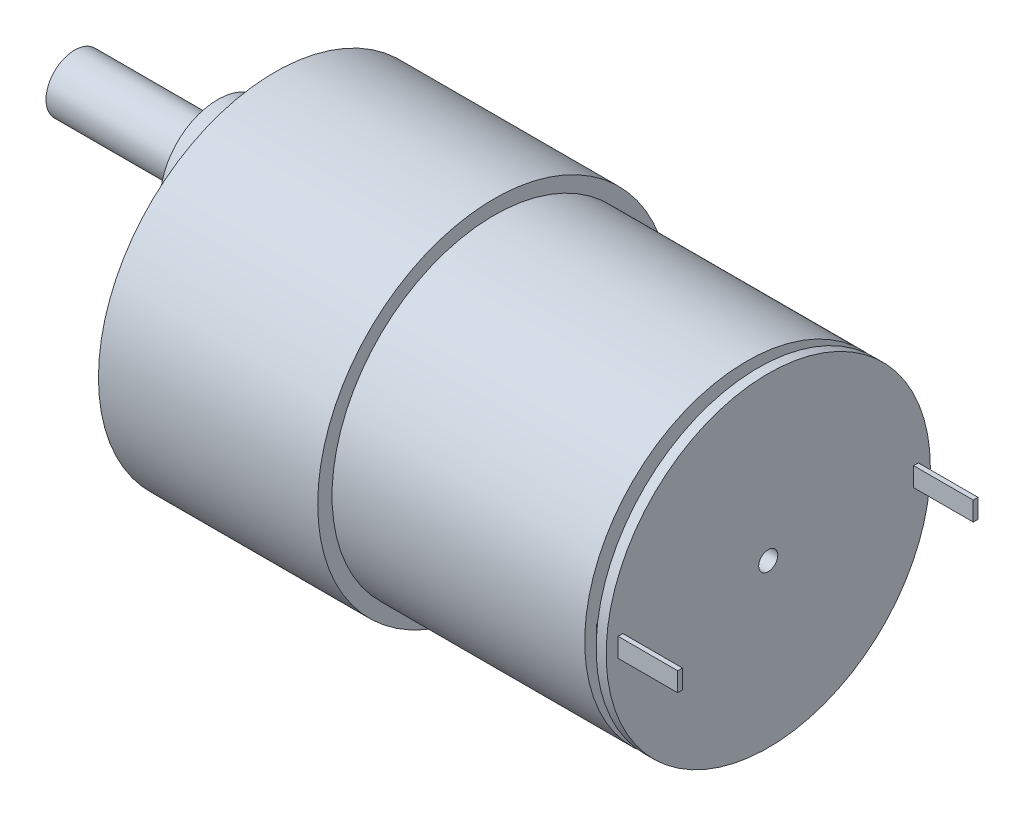
SolidWorks part; units mm, degrees
ref_plane "Front Plane" through (0, 0, 0) normal (0, 0, 1) x (1, 0, 0)
ref_plane "Top Plane" through (0, 0, 0) normal (0, 1, 0) x (1, 0, 0)
ref_plane "Right Plane" through (0, 0, 0) normal (1, 0, 0) x (0, 0, -1)
ref_plane "Plane1" through (41.25, 0, 0) normal (1, 0, 0) x (0, 0, -1)
sketch "Sketch1" plane through (41.25, 0, 0) normal (1, 0, 0) x (0, 0, -1)
  circle A0 centre (0, 0) radius 17
  dimension "D1" = 34
extrude "Boss-Extrude1" add sketch "Sketch1" against normal blind 1.05
sketch "Sketch2" plane through (40.2, 0, 0) normal (-1, 0, 0) x (0, 0, 1)
  line L0 (15.75, 1) -> (15.75, -1)
  line L1 (15.75, -1) -> (15.25, -1)
  line L2 (15.25, -1) -> (15.25, 1)
  line L3 (15.25, 1) -> (15.75, 1)
  line L4 (15.75, 1) -> (15.25, -1) construction
  line L5 (15.25, 1) -> (15.75, -1) construction
  line L6 (-15.25, 1) -> (-15.25, -1)
  line L7 (-15.25, -1) -> (-15.75, -1)
  line L8 (-15.75, -1) -> (-15.75, 1)
  line L9 (-15.75, 1) -> (-15.25, 1)
  line L10 (-15.25, 1) -> (-15.75, -1) construction
  line L11 (-15.75, 1) -> (-15.25, -1) construction
  circle A0 centre (0, 0) radius 15.5 construction
  point P7 (15.5, 0)
  point P12 (-15.5, 0)
  dimension "D3" = 31
  dimension "D1" = 2
  dimension "D2" = 0.5
extrude "Poles" add sketch "Sketch2" along normal blind 1.2 and the other way blind 7.3
sketch "Sketch3" plane through (40.2, 0, 0) normal (-1, 0, 0) x (0, 0, 1)
  circle A0 centre (0, 0) radius 1.5
extrude "Boss-Extrude3" add sketch "Sketch3" along normal blind 1.2
ref_plane "Plane2" through (39, 0, 0) normal (1, 0, 0) x (0, 0, -1)
sketch "Sketch5" plane through (39, 0, 0) normal (1, 0, 0) x (0, 0, -1)
  circle A2 centre (0, 0) radius 17
  dimension "D1" = 34
extrude "Boss-Extrude5" add sketch "Sketch5" against normal blind 26.5
ref_plane "Plane3" through (19, 0, 0) normal (1, 0, 0) x (0, 0, -1)
sketch "Sketch6" plane through (12.5, 0, 0) normal (1, 0, 0) x (0, 0, -1)
  circle A0 centre (0, 0) radius 18.5
  dimension "D1" = 37
extrude "Reductur" add sketch "Sketch6" against normal blind 21.5
sketch "Sketch35" plane through (-9, 0, 0) normal (-1, 0, 0) x (0, 0, 1)
  circle A0 centre (0, 0) radius 18.5
  circle A1 centre (0, 0) radius 18.5 construction
extrude "Endplate" add sketch "Sketch35" along normal blind 1.5
sketch "Sketch36" plane through (-10.5, 0, 0) normal (-1, 0, 0) x (0, 0, 1)
  circle A0 centre (0, 7) radius 6
  dimension "D2" = 12
  dimension "D1" = 7
extrude "Boss-Extrude25" add sketch "Sketch36" along normal blind 6
hole_wizard "Ø3.1 (3.1) Diameter Hole1" positions "Sketch38" profile "Sketch37" hole size "Ø3.1" standard "ANSI Metric"
sketch "Sketch38" plane through (-16.5, 0, 0) normal (-1, 0, 0) x (0, 0, 1)
  point P0 (0, 7)
sketch "Sketch37" plane through (-16.5, 7, 0) normal (0, 1, 0) x (0, 0, 1)
  line L0 (0, 0) -> (0, 2.2)
  line L1 (0, 2.2) -> (3, 2.2)
  line L2 (3, 2.2) -> (3, 0)
  line L5 (3, 0) -> (0, 0)
  line L10 (0, 2.2) -> (-3, 2.2) construction
  line L11 (0, -6.35) -> (0, 107.95) construction
  dimension "Hole Dia." = 6
  dimension "Hole Depth" = 2.2
  dimension "Drill Angle" = 180
hole_wizard "Ø2.0 (2) Diameter Hole1" positions "Sketch57" profile "Sketch56" hole size "Ø2.0" standard "ANSI Metric"
sketch "Sketch57" plane through (41.25, 0, 0) normal (1, 0, 0) x (0, 0, -1)
  point P0 (0, 0)
sketch "Sketch56" plane through (41.25, 0, 0) normal (0, 1, 0) x (0, 0, -1)
  line L0 (0, 0) -> (0, 2.25)
  line L1 (0, 2.25) -> (1, 2.25)
  line L2 (1, 2.25) -> (1, 0)
  line L5 (1, 0) -> (0, 0)
  line L10 (0, 2.25) -> (-1, 2.25) construction
  line L11 (0, -6.35) -> (0, 107.95) construction
  dimension "Hole Dia." = 2
  dimension "Hole Depth" = 2.25
  dimension "Drill Angle" = 180
ref_plane "Plane4" through (0, 0, 0) normal (0, 0, -1) x (-1, 0, 0)
sketch "Sketch39" [suppressed] plane through (-15.4, 0, 0) normal (-1, 0, 0) x (0, 0, 1)
  circle A0 centre (0, 7) radius 3
  dimension "D1" = 6
extrude "Shaft" [suppressed] add sketch "Sketch39" along normal blind 15
sketch "Sketch61" [suppressed] plane through (-30.4, 0, 0) normal (-1, 0, 0) x (0, 0, 1)
  line L4 (0, 4) -> (0, 9.4) construction
  line L5 (3, 9.4) -> (-3, 9.4)
  line L6 (-3, 9.4) -> (-3, 10)
  line L7 (-3, 10) -> (3, 10)
  line L8 (3, 10) -> (3, 9.4)
  circle A3 centre (0, 7) radius 3 construction
  point P7 (0, 9.4)
  dimension "D1" = 5.4
extrude "Flange" [suppressed] cut sketch "Sketch61" against normal blind 12
sketch "Mounting holes" plane through (-10.5, 0, 0) normal (-1, 0, 0) x (0, 0, 1)
  line L0 (-34.0879, 0) -> (34.0879, 0) construction
  line L1 (0, -11.3537) -> (0, 11.3537) construction
  line L2 (-13.4234, 7.75) -> (0, 0) construction
  line L3 (13.4234, 7.75) -> (0, 0) construction
  line L4 (0, -15.5) -> (0, 0) construction
  circle A0 centre (0, 0) radius 15.5 construction
  point P3 (-13.4234, 7.75)
  point P5 (0, 0)
  point P8 (-15.5, 0)
  point P11 (-7.75, 13.4234)
  point P15 (13.4234, 7.75)
  point P16 (7.75, 13.4234)
  point P18 (15.5, 0)
  point P19 (0, -15.5)
  point P20 (7.75, -13.4234)
  point P22 (-7.75, -13.4234)
  point P23 (0, 0)
  dimension "D1" = 31
  dimension "D2" = 3
hole_wizard "Ø3.0mm 定位孔1" positions "3DSketch1" profile "Sketch64" hole size "Ø3.0" standard "ISO"
sketch3d "3DSketch1"
  circle A0 centre (-10.5, 0, 0) radius 15.5 construction
  point P0 (-10.5, 0, -15.5)
  point P6 (-10.5, 13.4234, -7.75)
  point P9 (-10.5, 13.2729, 8.0051)
  point P13 (-26, 0, 0)
  point P17 (-10.5, 0, 15.5)
  point P23 (-10.5, -13.4234, 7.75)
  point P26 (-10.5, -13.4234, -7.75)
sketch "Sketch64" plane through (-10.5, 0, -15.5) normal (0, 1, 0) x (0, 0, 1)
  line L0 (0, 0) -> (0, 8.4013)
  line L1 (0, 8.4013) -> (1.5, 7.5)
  line L2 (1.5, 7.5) -> (1.5, 0)
  line L5 (1.5, 0) -> (0, 0)
  line L10 (0, 8.4013) -> (-1.5, 7.5) construction
  line L11 (0, -6.35) -> (0, 107.95) construction
  dimension "Hole Dia." = 3
  dimension "Hole Depth" = 7.5
  dimension "Drill Angle" = 118
split "Split1" [suppressed] bodies to split 160 161
sketch "草圖1" plane through (-10.5, 0, 0) normal (-1, 0, 0) x (0, 0, 1)
  circle A0 centre (0, 7) radius 3
extrude "填料-伸長1" add sketch "草圖1" along normal blind 21
